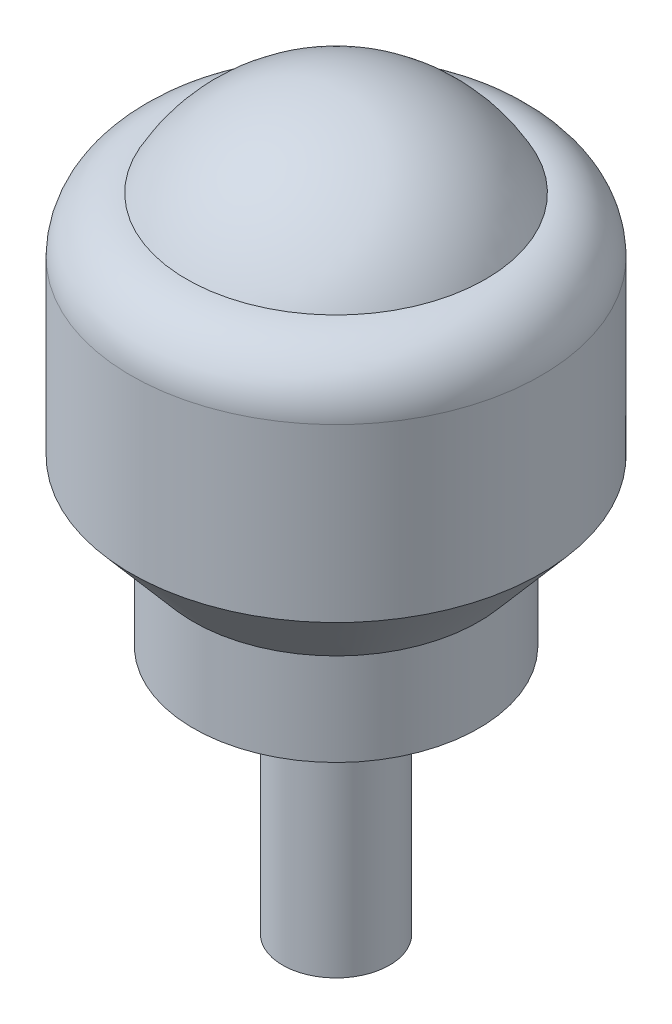
SolidWorks part; units mm, degrees
ref_plane "Plan de face" through (0, 0, 0) normal (0, 0, 1) x (1, 0, 0)
ref_plane "Plan de dessus" through (0, 0, 0) normal (0, 1, 0) x (1, 0, 0)
ref_plane "Plan de droite" through (0, 0, 0) normal (1, 0, 0) x (0, 0, -1)
sketch "Esquisse1" plane through (0, 0, 0) normal (0, 0, 1) x (1, 0, 0)
  line L0 (11.5, 1.4065) -> (11.5, -8.2067)
  line L1 (11.5, -8.2067) -> (8, -12.3014)
  line L2 (8, -12.3014) -> (8, -17.475)
  line L3 (8, -17.475) -> (3, -17.475)
  line L4 (3, -17.475) -> (3, -31.475)
  line L5 (3, -31.475) -> (0, -31.475)
  line L6 (0, 9.525) -> (0, -31.475) construction
  line L7 (0, 9.525) -> (0, -31.475)
  arc A0 (0, 9.525) -> (8.3815, 4.525) centre (0, 0) cw
  arc A1 (8.3815, 4.525) -> (11.5, 1.4065) centre (8.3815, 1.4065) cw
  dimension "D1" = 9.525
  dimension "D2" = 23
  dimension "D3" = 22
  dimension "D4" = 27
  dimension "D5" = 6
  dimension "D6" = 14
  dimension "D7" = 16
revolve "Révolution1" add sketch "Esquisse1" angle 360 about L6
